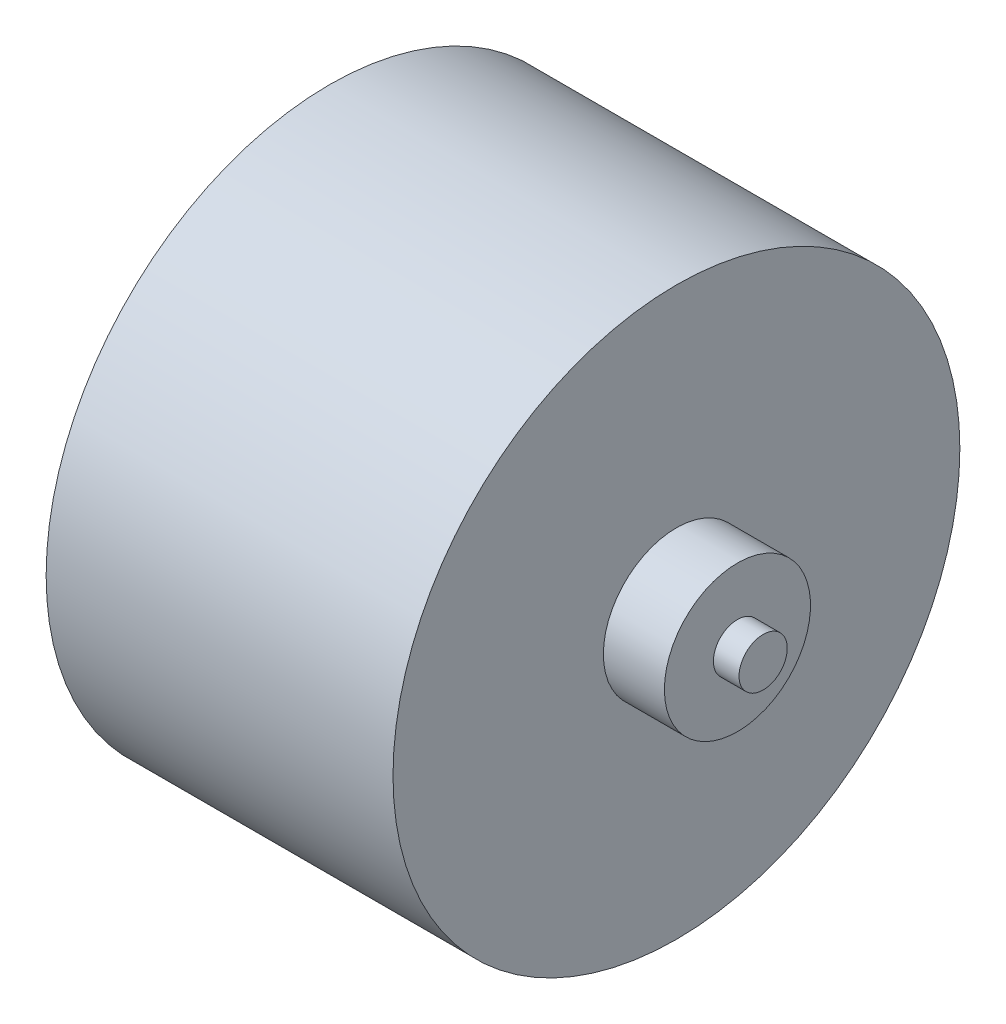
SolidWorks part; units mm, degrees
ref_plane "前视基准面" through (0, 0, 0) normal (0, 0, 1) x (1, 0, 0)
ref_plane "上视基准面" through (0, 0, 0) normal (0, 1, 0) x (1, 0, 0)
ref_plane "右视基准面" through (0, 0, 0) normal (1, 0, 0) x (0, 0, -1)
sketch "草图1" plane through (0, 0, 0) normal (0, 0, 1) x (1, 0, 0)
  line L0 (-47.2585, 0) -> (45.8887, 0) construction
  line L1 (-28.9528, 0) -> (-28.9528, 1.5)
  line L2 (-28.9528, 1.5) -> (-22.3528, 1.5)
  line L3 (-22.3528, 1.5) -> (-22.3528, 0)
  line L4 (-22.3528, 0) -> (-22.3528, 4.55)
  line L5 (-22.3528, 4.55) -> (-19.3528, 4.55)
  line L6 (-19.3528, 4.55) -> (-19.3528, 0)
  line L7 (-19.3528, 0) -> (-19.3528, 17.65)
  line L8 (-19.3528, 17.65) -> (2.2472, 17.65)
  line L9 (2.2472, 17.65) -> (2.2472, 0)
  line L10 (2.2472, 0) -> (2.2472, 4.55)
  line L11 (2.2472, 4.55) -> (6.0472, 4.55)
  line L12 (6.0472, 0) -> (6.0472, 1.5)
  line L13 (6.0472, 0) -> (6.0472, 4.55)
  line L14 (6.0472, 1.5) -> (7.6472, 1.5)
  line L15 (7.6472, 1.5) -> (7.6472, 0)
  line L16 (-28.9528, 0) -> (7.6472, 0)
  point P18 (5.5777, 5.3064)
  point P20 (7.4679, 2.2451)
  dimension "D1" = 6.6
  dimension "D2" = 3
  dimension "D3" = 21.6
  dimension "D4" = 3.8
  dimension "D5" = 1.6
  dimension "D6" = 1.5
  dimension "D7" = 4.55
  dimension "D8" = 17.65
  dimension "D9" = 4.55
  dimension "D10" = 1.5
revolve "旋转2" add sketch "草图1" angle 360 about L16
sketch "草图2" plane through (-19.3528, 0, 0) normal (-1, 0, 0) x (0, 0, 1)
  line L0 (-17.65, 0) -> (17.65, 0) construction
  line L1 (0, 17.65) -> (0, -17.65) construction
  circle A0 centre (0, 0) radius 17.65 construction
  circle A1 centre (0, 12.5) radius 2
  circle A2 centre (0, -12.5) radius 2
  circle A3 centre (-12.5, 0) radius 2
  circle A4 centre (12.5, 0) radius 2
  dimension "D2" = 4
  dimension "D4" = 4
  dimension "D1" = 25
  dimension "D3" = 25
extrude "切除-拉伸1" cut sketch "草图2" against normal blind 5
